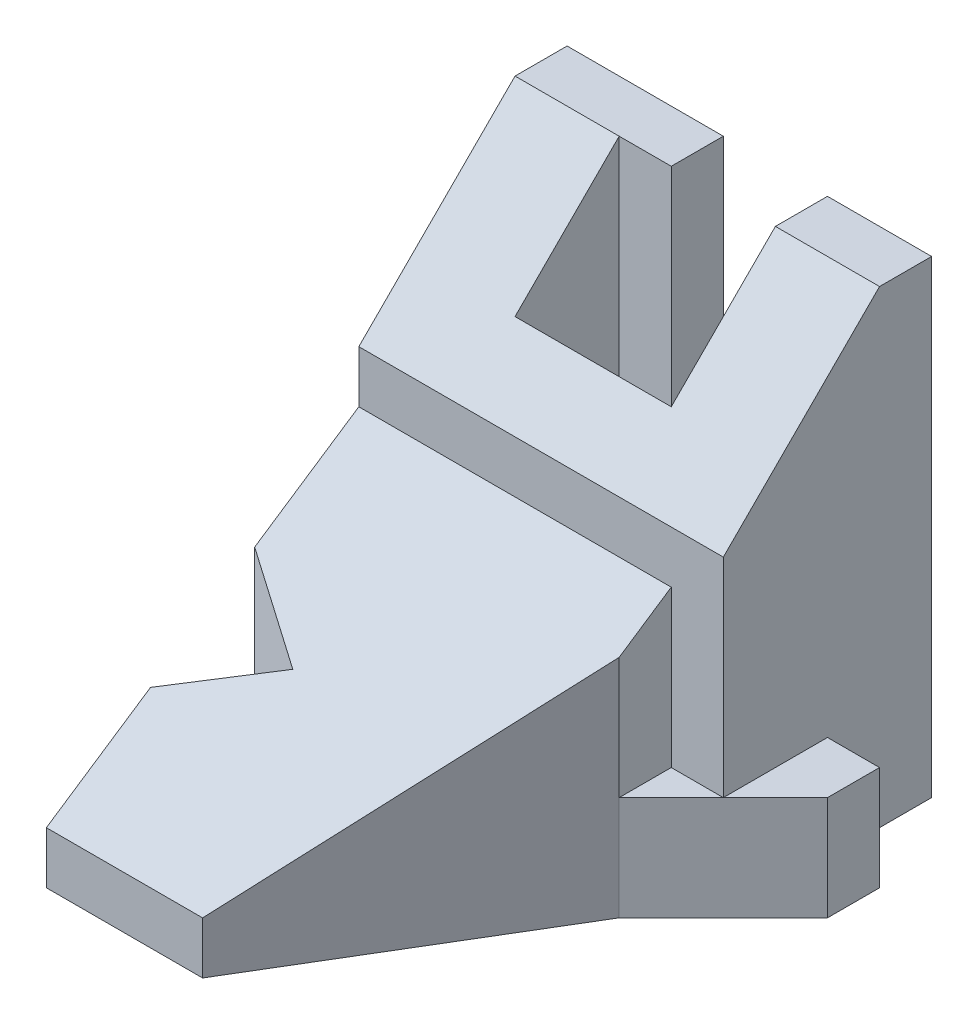
SolidWorks part; units mm, degrees
ref_plane "Front Plane" through (0, 0, 0) normal (0, 0, 1) x (1, 0, 0)
ref_plane "Top Plane" through (0, 0, 0) normal (0, 1, 0) x (1, 0, 0)
ref_plane "Right Plane" through (0, 0, 0) normal (1, 0, 0) x (0, 0, -1)
sketch "Sketch1" plane through (0, 0, 0) normal (0, 0, 1) x (1, 0, 0)
  line L1 (-17.5, 22.5) -> (17.5, 22.5)
  line L2 (-17.5, 22.5) -> (-17.5, -22.5)
  line L3 (-17.5, -22.5) -> (17.5, -22.5)
  line L4 (17.5, 22.5) -> (17.5, -22.5)
  line L5 (-17.5, 22.5) -> (17.5, -22.5) construction
  line L6 (-17.5, -22.5) -> (17.5, 22.5) construction
  point P0 (0, 0)
  dimension "D1" = 35
  dimension "D2" = 45
extrude "Boss-Extrude2" add sketch "Sketch1" along normal blind 20
sketch "Sketch3" plane through (0, 22.5, 0) normal (0, 1, 0) x (1, 0, 0)
  line L0 (7.5, 0) -> (7.5, -15)
  line L1 (17.5, 0) -> (-17.5, 0) construction
  line L2 (7.5, -15) -> (-12.5, -15)
  line L3 (-12.5, -15) -> (-12.5, -5)
  line L4 (-12.5, -5) -> (-7.5, -5)
  line L5 (-7.5, -5) -> (-7.5, 0)
  line L6 (-7.5, 0) -> (7.5, 0)
  line L8 (-17.5, -20) -> (-17.5, 0) construction
  point P10 (-13.6919, -3.1241)
  point P11 (13.4618, -5.7704)
  dimension "D1" = 15
  dimension "D2" = 10
  dimension "D3" = 10
  dimension "D4" = 5
  dimension "D5" = 10
extrude "Cut-Extrude1" cut sketch "Sketch3" against normal through all
sketch "Sketch4" plane through (17.5, 0, 0) normal (1, 0, 0) x (0, 0, -1)
  line L0 (-5, 22.5) -> (-20, 7.5)
  line L1 (-20, 22.5) -> (0, 22.5) construction
  line L2 (-20, -22.5) -> (-20, 22.5) construction
  line L3 (-20, 7.5) -> (-20, 22.5)
  line L4 (-20, 22.5) -> (-5, 22.5)
  dimension "D1" = 5
  dimension "D2" = 30
extrude "Cut-Extrude2" cut sketch "Sketch4" against normal through all
sketch "Sketch5" plane through (17.5, 0, 0) normal (1, 0, 0) x (0, 0, -1)
  line L0 (-20, -22.5) -> (-10, -22.5)
  line L1 (-20, -22.5) -> (0, -22.5) construction
  line L2 (-10, -22.5) -> (-10, -12.5)
  line L3 (-10, -12.5) -> (-20, -12.5)
  line L4 (-20, -22.5) -> (-20, 7.5) construction
  line L5 (-20, -12.5) -> (-20, -22.5)
  dimension "D1" = 10
  dimension "D2" = 10
extrude "Boss-Extrude3" add sketch "Sketch5" along normal blind 5
sketch "Sketch6" plane through (0, -12.5, 0) normal (0, 1, 0) x (1, 0, 0)
  line L0 (17.5, -20) -> (22.5, -15)
  line L1 (22.5, -10) -> (22.5, -20) construction
  line L2 (22.5, -15) -> (22.5, -20)
  line L3 (22.5, -20) -> (17.5, -20)
  dimension "D1" = 5
extrude "Cut-Extrude3" cut sketch "Sketch6" against normal through all
sketch "Sketch7" plane through (0, 0, 20) normal (0, 0, 1) x (1, 0, 0)
  line L0 (-17.5, 2.5) -> (12.5, 2.5)
  line L1 (-17.5, 7.5) -> (-17.5, -22.5) construction
  line L2 (12.5, 2.5) -> (12.5, -22.5)
  line L3 (-17.5, -22.5) -> (17.5, -22.5) construction
  line L4 (12.5, -22.5) -> (-17.5, -22.5)
  line L5 (-17.5, -22.5) -> (-17.5, 2.5)
  line L6 (17.5, -12.5) -> (17.5, 7.5) construction
  line L7 (-17.5, 7.5) -> (17.5, 7.5) construction
  dimension "D1" = 5
  dimension "D2" = 5
extrude "Boss-Extrude4" add sketch "Sketch7" along normal blind 30
sketch "Sketch8" plane through (0, 0, 20) normal (0, 0, 1) x (1, 0, 0)
  line L0 (17.5, -22.5) -> (17.5, -12.5)
  line L1 (17.5, -12.5) -> (12.5, -12.5)
  line L2 (12.5, -22.5) -> (12.5, 2.5) construction
  line L3 (12.5, -12.5) -> (12.5, -22.5)
  line L4 (12.5, -22.5) -> (17.5, -22.5)
extrude "Boss-Extrude5" add sketch "Sketch8" along normal blind 5
sketch "Sketch9" plane through (0, -12.5, 0) normal (0, 1, 0) x (1, 0, 0)
  line L0 (17.5, -20) -> (12.5, -25)
  line L1 (12.5, -25) -> (17.5, -25)
  line L2 (17.5, -25) -> (17.5, -20)
extrude "Cut-Extrude4" cut sketch "Sketch9" against normal through all
sketch "Sketch11" plane through (-7.5, 0, 0) normal (1, 0, 0) x (0, 0, -1)
  line L0 (0, 22.5) -> (0, -22.5)
  line L1 (0, -22.5) -> (-5, -22.5)
  line L2 (-5, -22.5) -> (-5, 22.5)
  line L3 (-5, 22.5) -> (0, 22.5)
extrude "Boss-Extrude6" add sketch "Sketch11" along normal blind 5
sketch "Sketch12" plane through (-12.5, 0, 0) normal (1, 0, 0) x (0, 0, -1)
  line L0 (-5, 22.5) -> (-5, -22.5)
  line L1 (-5, -22.5) -> (-15, -22.5)
  line L2 (-15, -22.5) -> (-15, 12.5)
  line L3 (-15, 12.5) -> (-5, 22.5)
extrude "Boss-Extrude7" add sketch "Sketch12" along normal blind 5
sketch "Sketch13" plane through (0, 2.5, 0) normal (0, 1, 0) x (1, 0, 0)
  line L0 (12.5, -25) -> (-2.5, -50)
  line L1 (12.5, -50) -> (-17.5, -50) construction
  line L2 (-2.5, -50) -> (12.5, -50)
  line L3 (12.5, -50) -> (12.5, -25)
  dimension "D1" = 15
extrude "Cut-Extrude7" cut sketch "Sketch13" against normal through all
sketch "Sketch14" plane through (0, 2.5, 0) normal (0, 1, 0) x (1, 0, 0)
  line L0 (-17.5, -30) -> (-8.8397, -35)
  line L1 (-17.5, -50) -> (-17.5, -20) construction
  line L2 (-8.8397, -35) -> (-17.5, -40)
  line L3 (-17.5, -40) -> (-17.5, -30)
  line L4 (-17.5, -20) -> (17.5, -20) construction
  point P11 (0.7983, -32.0727)
  dimension "D1" = 10
  dimension "D2" = 10
  dimension "D3" = 15
  dimension "D4" = 10
extrude "Cut-Extrude8" cut sketch "Sketch14" against normal through all
ref_plane "Plane1" through (-17.5, 0, 0) normal (1, 0, 0) x (0, 0, -1)
sketch "Sketch15" plane through (-17.5, 0, 0) normal (1, 0, 0) x (0, 0, -1)
  line L0 (-20, 2.5) -> (-50, -17.5)
  line L1 (-50, 2.5) -> (-50, -22.5) construction
  line L2 (-50, -17.5) -> (-50, 2.5)
  line L3 (-50, 2.5) -> (-20, 2.5)
  dimension "D1" = 5
extrude "Cut-Extrude11" cut sketch "Sketch15" along normal through all
